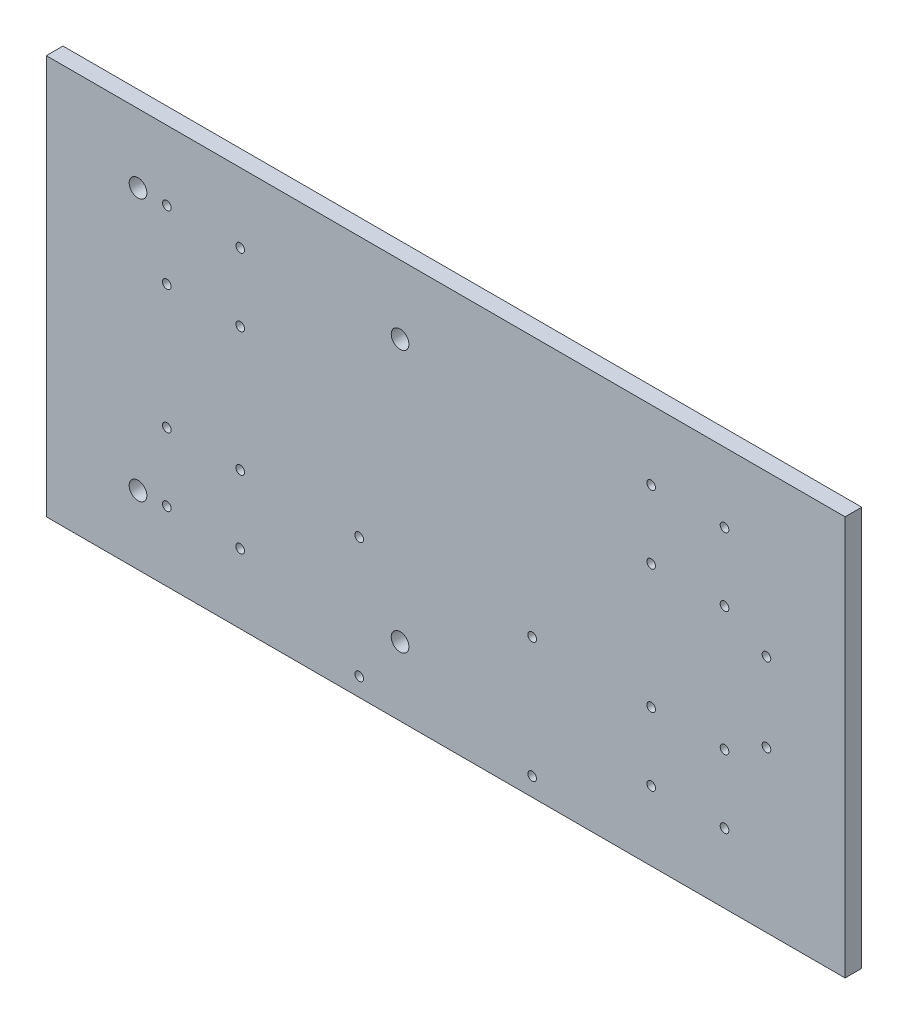
SolidWorks part; units mm, degrees
ref_plane "Front Plane" through (0, 0, 0) normal (0, 0, 1) x (1, 0, 0)
ref_plane "Top Plane" through (0, 0, 0) normal (0, 1, 0) x (1, 0, 0)
ref_plane "Right Plane" through (0, 0, 0) normal (1, 0, 0) x (0, 0, -1)
sketch "Sketch1" plane through (0, 0, 0) normal (0, 0, 1) x (1, 0, 0)
  line L1 (-152.4, 76.2) -> (152.4, 76.2)
  line L2 (-152.4, 76.2) -> (-152.4, -76.2)
  line L3 (-152.4, -76.2) -> (152.4, -76.2)
  line L4 (152.4, 76.2) -> (152.4, -76.2)
  line L5 (-152.4, 76.2) -> (152.4, -76.2) construction
  line L6 (-152.4, -76.2) -> (152.4, 76.2) construction
  point P0 (0, 0)
  dimension "D1" = 152.4
  dimension "D2" = 304.8
extrude "Boss-Extrude1" add sketch "Sketch1" along normal blind 6.35
sketch "Sketch2" plane through (0, 0, 0) normal (0, 0, -1) x (-1, 0, 0)
  point P0 (106.4, 49.7)
  point P1 (106.4, 23.7)
  point P3 (78.4, 23.7)
  point P5 (78.4, 49.7)
  point P7 (106.4, -23.7)
  point P9 (106.4, -49.7)
  point P11 (78.4, -23.7)
  point P13 (78.4, -49.7)
  point P15 (-78.4, 49.7)
  point P17 (-106.4, 49.7)
  point P19 (-106.4, 23.7)
  point P21 (-78.4, 23.7)
  point P23 (-78.4, -23.7)
  point P25 (-106.4, -23.7)
  point P27 (-106.4, -49.7)
  point P29 (-78.4, -49.7)
hole_wizard "M4x0.7 Tapped Hole1" positions "3DSketch2" profile "Sketch4" tap size "M4x0.7" standard "ANSI Metric"
sketch3d "3DSketch2"
  point P0 (78.4, 49.7, 0)
  point P3 (78.4, 23.7, 0)
  point P6 (106.4, 23.7, 0)
  point P9 (106.4, 49.7, 0)
  point P12 (78.4, -23.7, 0)
  point P15 (78.4, -49.7, 0)
  point P18 (106.4, -23.7, 0)
  point P21 (106.4, -49.7, 0)
  point P24 (-106.4, 49.7, 0)
  point P27 (-78.4, 49.7, 0)
  point P30 (-78.4, 23.7, 0)
  point P33 (-106.4, 23.7, 0)
  point P36 (-106.4, -23.7, 0)
  point P39 (-106.4, -49.7, 0)
  point P42 (-78.4, -23.7, 0)
  point P45 (-78.4, -49.7, 0)
sketch "Sketch4" plane through (78.4, 49.7, 0) normal (1, 0, 0) x (0, 1, 0)
  line L0 (0, 0) -> (0, 11.75)
  line L1 (0, 11.75) -> (1.65, 10.1)
  line L2 (1.65, 10.1) -> (1.65, 0)
  line L5 (1.65, 0) -> (0, 0)
  line L10 (0, 11.75) -> (-1.65, 10.1) construction
  line L11 (0, -6.35) -> (0, 107.95) construction
  dimension "Tap Drill Dia." = 3.3
  dimension "Tap Drill Depth" = 10.1
  dimension "Drill Angle" = 90
cosmetic thread "Hole Thread1" parameters "D1"=6.35, "D2"=4
cosmetic thread "Hole Thread2" parameters "D1"=6.35, "D2"=4
cosmetic thread "Hole Thread3" parameters "D1"=6.35, "D2"=4
cosmetic thread "Hole Thread4" parameters "D1"=6.35, "D2"=4
cosmetic thread "Hole Thread5" parameters "D1"=6.35, "D2"=4
cosmetic thread "Hole Thread6" parameters "D1"=6.35, "D2"=4
cosmetic thread "Hole Thread7" parameters "D1"=6.35, "D2"=4
cosmetic thread "Hole Thread8" parameters "D1"=6.35, "D2"=4
cosmetic thread "Hole Thread9" parameters "D1"=6.35, "D2"=4
cosmetic thread "Hole Thread10" parameters "D1"=6.35, "D2"=4
cosmetic thread "Hole Thread11" parameters "D1"=6.35, "D2"=4
cosmetic thread "Hole Thread12" parameters "D1"=6.35, "D2"=4
cosmetic thread "Hole Thread13" parameters "D1"=6.35, "D2"=4
cosmetic thread "Hole Thread14" parameters "D1"=6.35, "D2"=4
cosmetic thread "Hole Thread15" parameters "D1"=6.35, "D2"=4
cosmetic thread "Hole Thread16" parameters "D1"=6.35, "D2"=4
sketch "Sketch5" plane through (0, 0, 6.35) normal (0, 0, 1) x (1, 0, 0)
  circle A0 centre (-117.4, -50.0001) radius 3.375
  circle A1 centre (-117.4, 49.9999) radius 3.375
  circle A2 centre (-17.4, -50.0001) radius 3.375
  circle A3 centre (-17.4, 49.9999) radius 3.375
  dimension "D1" = 6.75
  dimension "D2" = 6.75
  dimension "D3" = 6.75
  dimension "D4" = 6.75
extrude "Cut-Extrude1" cut sketch "Sketch5" against normal through all
sketch "Sketch6" plane through (0, 0, 0) normal (0, 0, -1) x (-1, 0, 0)
  circle A0 centre (33, -69.2) radius 1.65
  circle A1 centre (33, -23.2) radius 1.65
  circle A2 centre (-33, -23.2) radius 1.65
  circle A3 centre (-33, -69.2) radius 1.65
  dimension "D1" = 3.3
  dimension "D2" = 3.3
  dimension "D3" = 3.3
  dimension "D4" = 3.3
extrude "Cut-Extrude2" cut sketch "Sketch6" against normal through all
sketch "Sketch7" plane through (0, 0, 6.35) normal (0, 0, 1) x (1, 0, 0)
  line L0 (152.4, 0) -> (39.8145, 0) construction
  line L1 (152.4, -76.2) -> (152.4, 76.2) construction
  line L2 (122.4, 76.2) -> (122.4, -76.2) construction
  line L3 (152.4, 76.2) -> (-152.4, 76.2) construction
  line L4 (-152.4, -76.2) -> (152.4, -76.2) construction
  circle A0 centre (122.4, 15) radius 1.65
  circle A1 centre (122.4, -15) radius 1.65
  dimension "D1" = 3.3
  dimension "D2" = 3.3
  dimension "D3" = 15
  dimension "D4" = 15
  dimension "D5" = 30
extrude "Cut-Extrude3" cut sketch "Sketch7" against normal through all
